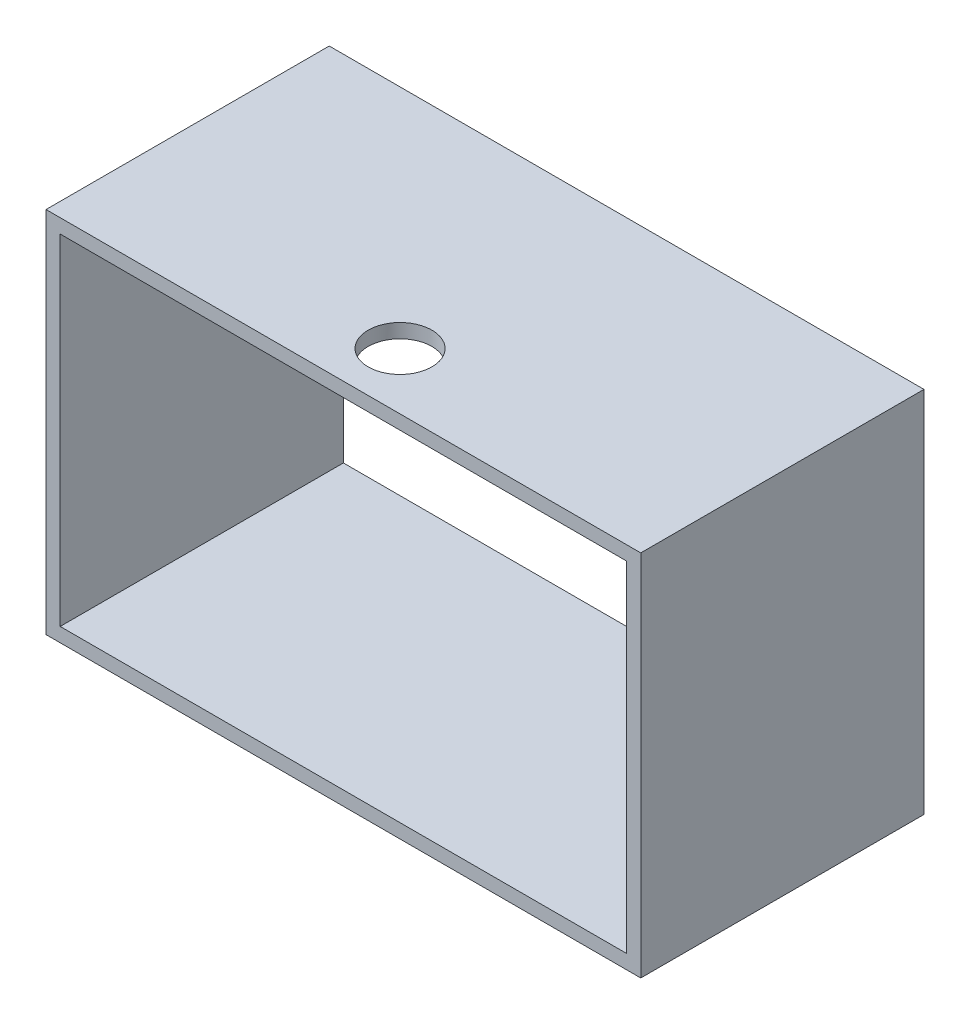
SolidWorks part; units mm, degrees
ref_plane "Front Plane" through (0, 0, 0) normal (0, 0, 1) x (1, 0, 0)
ref_plane "Top Plane" through (0, 0, 0) normal (0, 1, 0) x (1, 0, 0)
ref_plane "Right Plane" through (0, 0, 0) normal (1, 0, 0) x (0, 0, -1)
sketch "Sketch1" plane through (0, 0, 0) normal (0, 0, 1) x (1, 0, 0)
  line L0 (6.35, 6.35) -> (6.35, 158.75)
  line L1 (0, 0) -> (266.7, 0)
  line L2 (0, 0) -> (0, 165.1)
  line L3 (0, 165.1) -> (266.7, 165.1)
  line L4 (266.7, 0) -> (266.7, 165.1)
  line L5 (6.35, 158.75) -> (260.35, 158.75)
  line L6 (260.35, 6.35) -> (260.35, 158.75)
  line L7 (6.35, 6.35) -> (260.35, 6.35)
  dimension "D1" = 266.7
  dimension "D2" = 165.1
  dimension "D3" = 6.35
extrude "Boss-Extrude1" add sketch "Sketch1" along normal blind 215.9
sketch "Sketch4" plane through (266.7, 0, 0) normal (1, 0, 0) x (0, 0, -1)
  line L0 (-215.9, 0) -> (0, 0) construction
  line L1 (-215.9, 165.1) -> (-127, 165.1)
  line L2 (-215.9, 165.1) -> (-215.9, 0)
  line L3 (-215.9, 0) -> (-127, 0)
  line L4 (-127, 165.1) -> (-127, 0)
  dimension "D1" = 88.9
extrude "Cut-Extrude2" cut sketch "Sketch4" against normal through all
sketch "Sketch3" plane through (0, 165.1, 0) normal (0, 1, 0) x (1, 0, 0)
  line L1 (0, 0) -> (-25.4, 0)
  line L2 (0, 0) -> (0, -50.8)
  line L3 (0, -50.8) -> (-25.4, -50.8)
  line L4 (-25.4, 0) -> (-25.4, -50.8)
  line L5 (266.7, 0) -> (292.1, 0)
  line L6 (266.7, 0) -> (266.7, -50.8)
  line L7 (266.7, -50.8) -> (292.1, -50.8)
  line L8 (292.1, 0) -> (292.1, -50.8)
  dimension "D1" = 25.4
  dimension "D2" = 50.8
extrude "Boss-Extrude2" [suppressed] add sketch "Sketch3" along normal mid plane 254
sketch "Sketch5" plane through (0, 165.1, 0) normal (0, 1, 0) x (1, 0, 0)
  line L0 (0, -127) -> (266.7, -127) construction
  line L1 (0, -50.8) -> (-50000, -50.8) construction
  line L3 (266.7, 0) -> (0, 0) construction
  circle A0 centre (133.35, -101.6) radius 14.2875
  point P4 (133.35, -127)
  dimension "D1" = 28.575
  dimension "D2" = 50.8
  dimension "D3" = 50.8
extrude "Cut-Extrude3" cut sketch "Sketch5" against normal up to next
